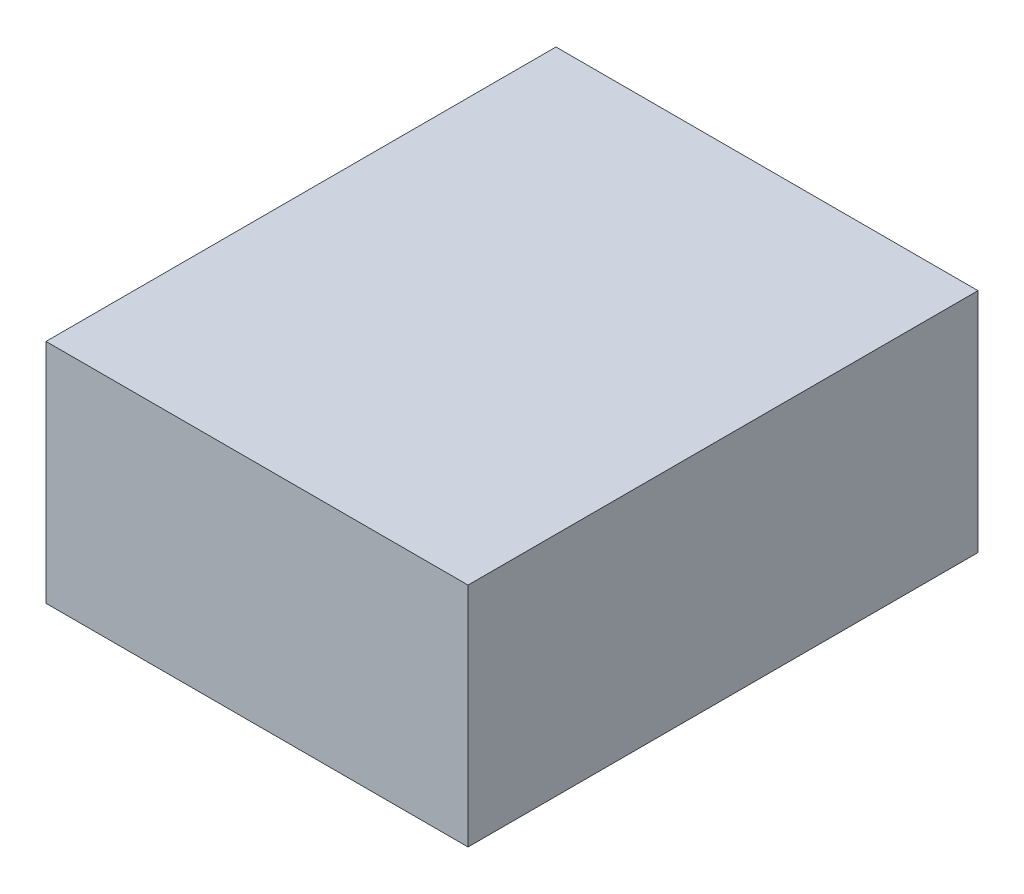
SolidWorks part; units mm, degrees
ref_plane "Front Plane" through (0, 0, 0) normal (0, 0, 1) x (1, 0, 0)
ref_plane "Top Plane" through (0, 0, 0) normal (0, 1, 0) x (1, 0, 0)
ref_plane "Right Plane" through (0, 0, 0) normal (1, 0, 0) x (0, 0, -1)
sketch "Sketch1" plane through (0, 0, 0) normal (0, 0, 1) x (1, 0, 0)
  line L1 (120, -64.5) -> (-120, -64.5)
  line L2 (120, -64.5) -> (120, 64.5)
  line L3 (120, 64.5) -> (-120, 64.5)
  line L4 (-120, -64.5) -> (-120, 64.5)
  line L5 (120, -64.5) -> (-120, 64.5) construction
  line L6 (120, 64.5) -> (-120, -64.5) construction
  point P0 (0, 0)
extrude "Boss-Extrude1" add sketch "Sketch1" along normal blind 290 contours L2 L3 L4 L1
